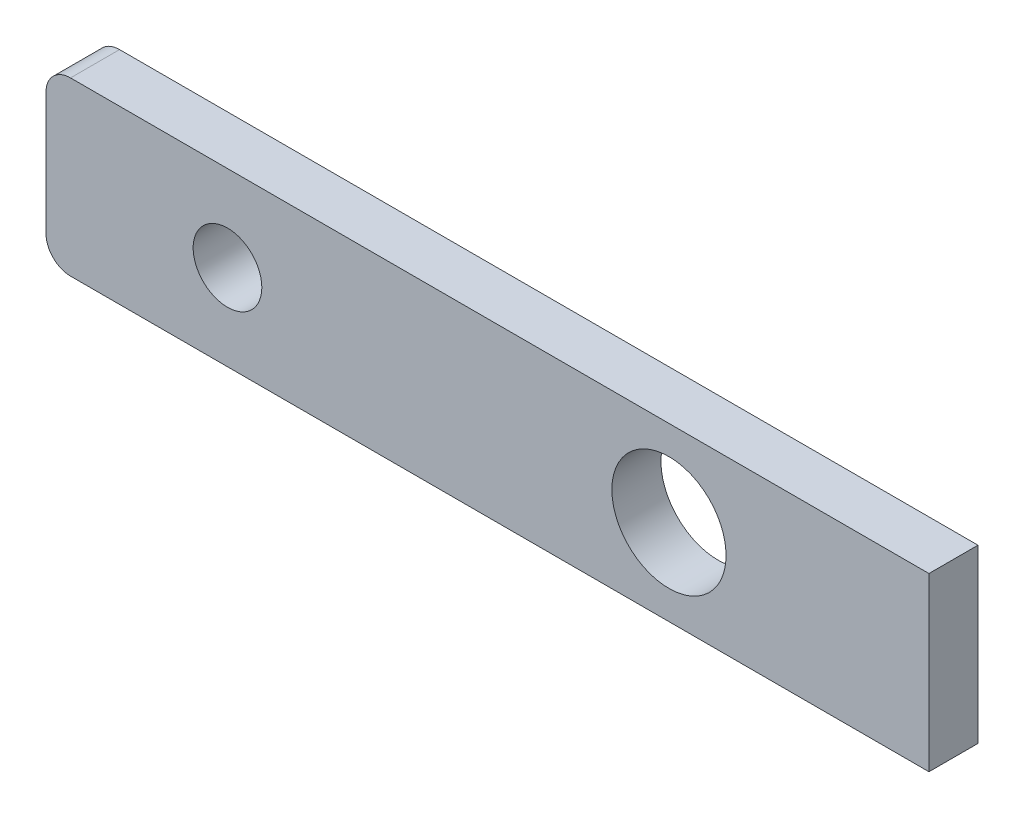
SolidWorks part; units mm, degrees
material "Aluminum Bronze"
ref_plane "Front Plane" through (0, 0, 0) normal (0, 0, 1) x (1, 0, 0)
ref_plane "Top Plane" through (0, 0, 0) normal (0, 1, 0) x (1, 0, 0)
ref_plane "Right Plane" through (0, 0, 0) normal (1, 0, 0) x (0, 0, -1)
sketch "Sketch2" plane through (0, 0, 0) normal (0, 0, 1) x (1, 0, 0)
  line L1 (-9, 1.75) -> (9, 1.75)
  line L2 (-9, 1.75) -> (-9, -1.75)
  line L3 (-9, -1.75) -> (9, -1.75)
  line L4 (9, 1.75) -> (9, -1.75)
  line L5 (-9, 1.75) -> (9, -1.75) construction
  line L6 (-9, -1.75) -> (9, 1.75) construction
  point P0 (0, 0)
  dimension "D1" = 3.5
  dimension "D2" = 18
extrude "Boss-Extrude1" add sketch "Sketch2" along normal blind 1
sketch "Sketch3" plane through (0, 0, 1) normal (0, 0, 1) x (1, 0, 0)
  line L0 (-5.3, 0) -> (-9, 0) construction
  line L1 (-9, 1.75) -> (-9, -1.75) construction
  circle A0 centre (-5.3, 0) radius 0.7
  dimension "D1" = 1.4
  dimension "D2" = 3.7
extrude "Cut-Extrude1" cut sketch "Sketch3" against normal through all
fillet "Fillet1" radius 0.5 2 edges at (-9, -1.75, 0.5) (-9, 1.75, 0.5)
sketch "Sketch4" plane through (0, 0, 0) normal (0, 0, -1) x (-1, 0, 0)
  line L0 (-9, 0) -> (9, 0) construction
  line L4 (-9, -1.75) -> (8.5, -1.75)
  line L5 (9, -1.25) -> (9, 1.25)
  line L6 (8.5, 1.75) -> (-9, 1.75)
  line L7 (-9, 1.75) -> (-9, -1.75)
  line L8 (-9, -1.75) -> (8.5, -1.75)
  line L9 (9, -1.25) -> (9, 1.25)
  line L10 (8.5, 1.75) -> (-9, 1.75)
  line L11 (-9, 1.75) -> (-9, -1.75)
  circle A0 centre (-3.7, 0) radius 1.164
  arc A2 (8.5, -1.75) -> (9, -1.25) centre (8.5, -1.25) ccw
  arc A3 (9, 1.25) -> (8.5, 1.75) centre (8.5, 1.25) ccw
  arc A4 (8.5, -1.75) -> (9, -1.25) centre (8.5, -1.25) ccw
  arc A5 (9, 1.25) -> (8.5, 1.75) centre (8.5, 1.25) ccw
  dimension "D2" = 2.328
  dimension "D1" = 0
extrude "Cut-Extrude3" cut sketch "Sketch4" against normal through all flip side to cut
